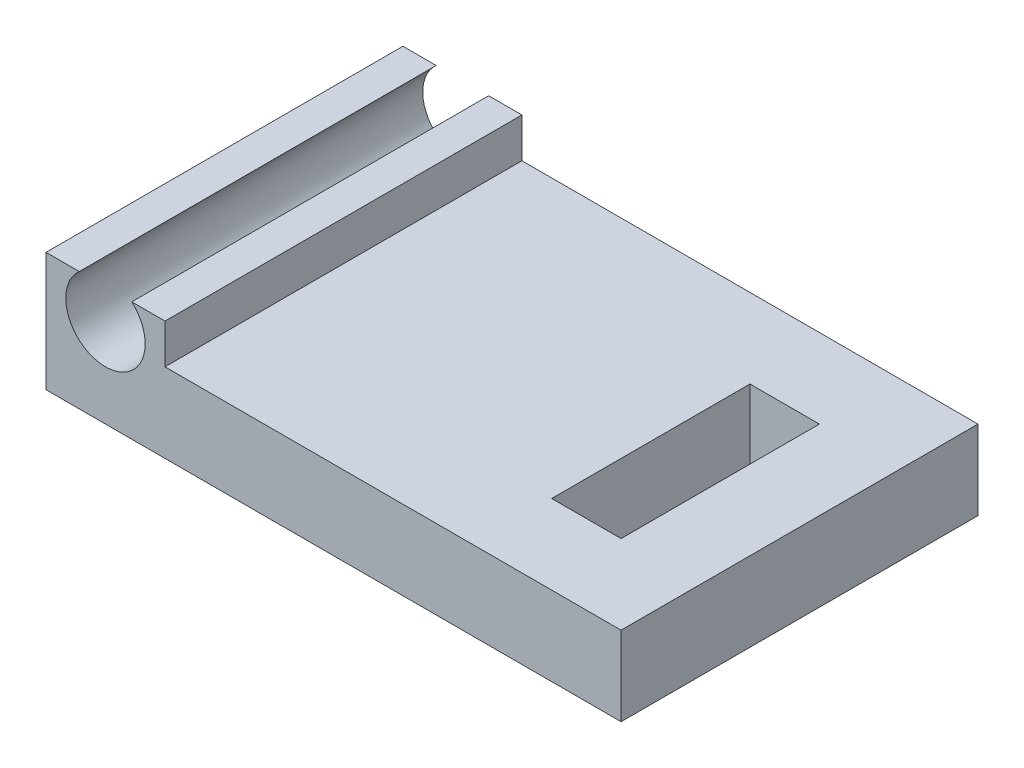
SolidWorks part; units mm, degrees
ref_plane "Front Plane" through (0, 0, 0) normal (0, 0, 1) x (1, 0, 0)
ref_plane "Top Plane" through (0, 0, 0) normal (0, 1, 0) x (1, 0, 0)
ref_plane "Right Plane" through (0, 0, 0) normal (1, 0, 0) x (0, 0, -1)
sketch "Sketch1" plane through (0, 0, 0) normal (0, 1, 0) x (1, 0, 0)
  line L1 (-7.366, 4.572) -> (7.366, 4.572)
  line L2 (-7.366, 4.572) -> (-7.366, -4.572)
  line L3 (-7.366, -4.572) -> (7.366, -4.572)
  line L4 (7.366, 4.572) -> (7.366, -4.572)
  line L5 (-7.366, 4.572) -> (7.366, -4.572) construction
  line L6 (-7.366, -4.572) -> (7.366, 4.572) construction
  line L7 (3.556, 2.54) -> (5.334, 2.54)
  line L8 (3.556, 2.54) -> (3.556, -2.54)
  line L9 (3.556, -2.54) -> (5.334, -2.54)
  line L10 (5.334, 2.54) -> (5.334, -2.54)
  point P0 (0, 0)
  dimension "D1" = 5.08
  dimension "D2" = 1.778
  dimension "D3" = 2.032
  dimension "D4" = 2.032
  dimension "D5" = 2.032
  dimension "D6" = 12.7
extrude "Boss-Extrude1" add sketch "Sketch1" along normal blind 2.032
sketch "Sketch2" plane through (0, 2.032, 0) normal (0, 1, 0) x (1, 0, 0)
  line L0 (-7.366, -4.572) -> (7.366, -4.572) construction
  line L1 (-7.366, 4.572) -> (-4.318, 4.572)
  line L2 (-7.366, 4.572) -> (-7.366, -4.572)
  line L3 (-7.366, -4.572) -> (-4.318, -4.572)
  line L4 (-4.318, 4.572) -> (-4.318, -4.572)
  dimension "D1" = 3.048
extrude "Boss-Extrude2" add sketch "Sketch2" along normal blind 1.016
sketch "Sketch3" plane through (0, 0, 4.572) normal (0, 0, 1) x (1, 0, 0)
  line L0 (-7.366, 3.048) -> (-4.318, 3.048) construction
  line L1 (-7.366, 3.048) -> (-7.366, 0) construction
  circle A0 centre (-5.842, 2.286) radius 1.016
  dimension "D1" = 0.762
  dimension "D2" = 2.032
  dimension "D3" = 1.524
extrude "Cut-Extrude1" cut sketch "Sketch3" against normal through all
